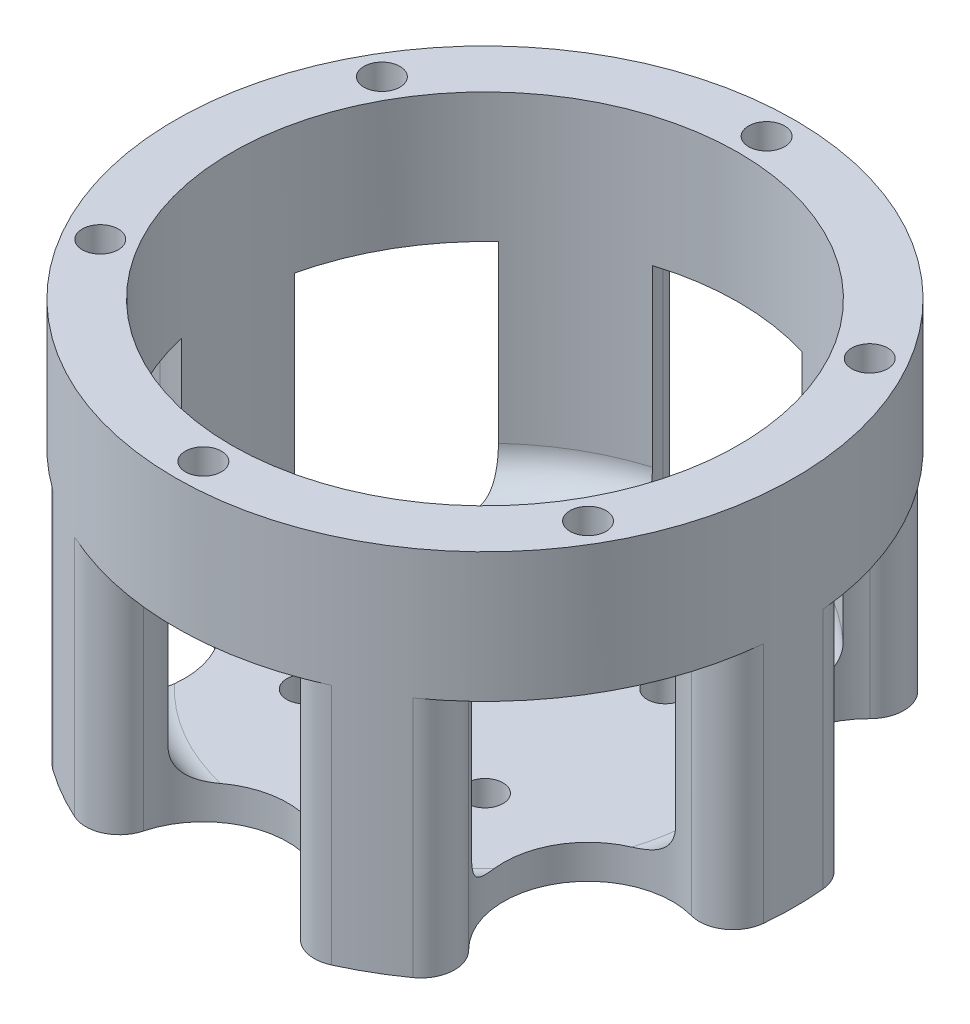
SolidWorks part; units mm, degrees
ref_plane "Front Plane" through (0, 0, 0) normal (0, 0, 1) x (1, 0, 0)
ref_plane "Top Plane" through (0, 0, 0) normal (0, 1, 0) x (1, 0, 0)
ref_plane "Right Plane" through (0, 0, 0) normal (1, 0, 0) x (0, 0, -1)
sketch "Sketch1" plane through (0, 0, 0) normal (0, 1, 0) x (1, 0, 0)
  circle A0 centre (0, 0) radius 27.5
  circle A1 centre (0, 0) radius 25 construction
  circle A2 centre (0, 25) radius 1.6
  circle A3 centre (21.6506, 12.5) radius 1.6
  circle A4 centre (21.6506, -12.5) radius 1.6
  circle A5 centre (0, -25) radius 1.6
  circle A6 centre (-21.6506, -12.5) radius 1.6
  circle A7 centre (-21.6506, 12.5) radius 1.6
  point P19 (0, 0)
  point P31 (0, 0)
  dimension "D1" = 55
  dimension "D2" = 50
  dimension "D3" = 3.2
  dimension "D4" = 6
extrude "Boss-Extrude1" add sketch "Sketch1" along normal blind 33
sketch "Sketch2" plane through (0, 33, 0) normal (0, 1, 0) x (1, 0, 0)
  circle A0 centre (0, 0) radius 22.5
  dimension "D1" = 45
extrude "Cut-Extrude1" cut sketch "Sketch2" against normal blind 30
sketch "Sketch3" plane through (0, 0, 0) normal (0, -1, 0) x (1, 0, 0)
  circle A0 centre (0, 25) radius 7.5
  dimension "D1" = 15
extrude "Cut-Extrude2" cut sketch "Sketch3" against normal blind 21.5
fillet "Fillet1" radius 3 2 edges at (-7.3485, 10.75, 26.5) (7.3485, 10.75, 26.5)
pattern_circular "CirPattern1" count 6 over 360 about axis through (0, 0, 0) along (0, 1, 0) of "Cut-Extrude2", "Fillet1"
sketch "Sketch5" plane through (0, 0, 0) normal (0, -1, 0) x (1, 0, 0)
  line L1 (-8, -8) -> (8, -8) construction
  line L2 (-8, -8) -> (-8, 8) construction
  line L3 (-8, 8) -> (8, 8) construction
  line L4 (8, -8) -> (8, 8) construction
  line L5 (-8, -8) -> (8, 8) construction
  line L6 (-8, 8) -> (8, -8) construction
  circle A0 centre (-8, 8) radius 1.6
  circle A1 centre (8, 8) radius 1.6
  circle A2 centre (8, -8) radius 1.6
  circle A3 centre (-8, -8) radius 1.6
  point P0 (0, 0)
  dimension "D3" = 3.2
  dimension "D1" = 16
extrude "Cut-Extrude3" cut sketch "Sketch5" against normal blind 10
fillet "Fillet4" radius 3 6 edges at (22.5, 3, 0) (11.25, 3, -19.4856) (11.25, 3, 19.4856) (-11.25, 3, -19.4856) (-22.5, 3, 0) (-11.25, 3, 19.4856)
